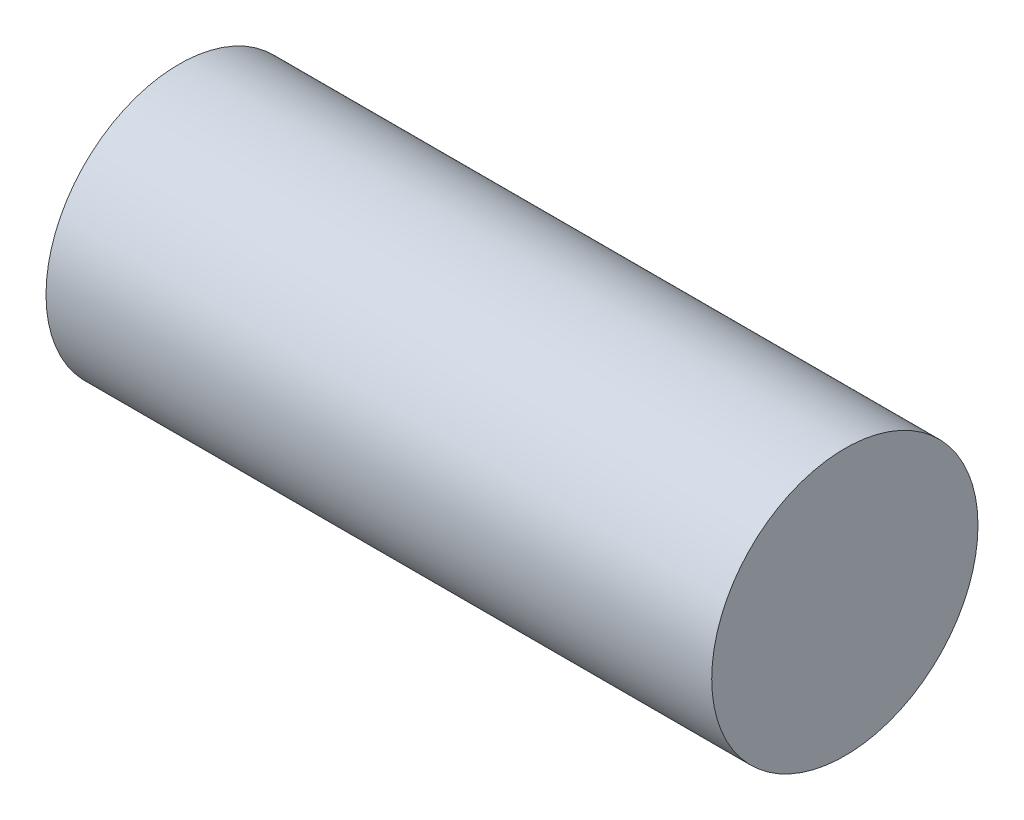
SolidWorks part; units mm, degrees
material "1023 al carbonio, lamiera (SS)"
ref_plane "Piano frontale" through (0, 0, 0) normal (0, 0, 1) x (1, 0, 0)
ref_plane "Piano superiore" through (0, 0, 0) normal (0, 1, 0) x (1, 0, 0)
ref_plane "Piano destro" through (0, 0, 0) normal (1, 0, 0) x (0, 0, -1)
sketch "Schizzo1" plane through (0, 0, 0) normal (0, 0, 1) x (1, 0, 0)
  line L1 (0, 0) -> (40, 0)
  line L2 (0, 0) -> (0, 8)
  line L3 (0, 8) -> (40, 8)
  line L4 (40, 0) -> (40, 8)
  dimension "D1" = 8
  dimension "D2" = 40
revolve "Rivoluzione1" add sketch "Schizzo1" angle 360 about L3
